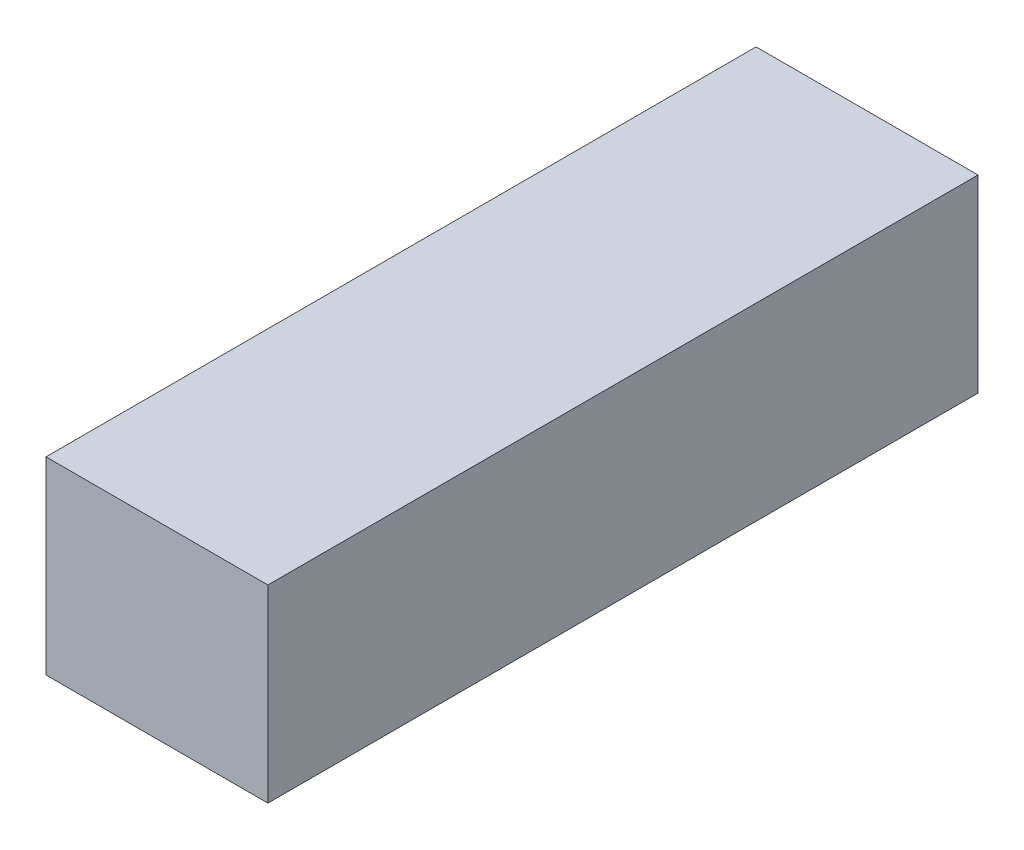
SolidWorks part; units mm, degrees
ref_plane "Front Plane" through (0, 0, 0) normal (0, 0, 1) x (1, 0, 0)
ref_plane "Top Plane" through (0, 0, 0) normal (0, 1, 0) x (1, 0, 0)
ref_plane "Right Plane" through (0, 0, 0) normal (1, 0, 0) x (0, 0, -1)
sketch "Sketch1" plane through (0, 0, 0) normal (0, 0, 1) x (1, 0, 0)
  line L1 (-17.5, -14.9) -> (17.5, -14.9)
  line L2 (-17.5, -14.9) -> (-17.5, 14.9)
  line L3 (-17.5, 14.9) -> (17.5, 14.9)
  line L4 (17.5, -14.9) -> (17.5, 14.9)
  line L5 (-17.5, -14.9) -> (17.5, 14.9) construction
  line L6 (-17.5, 14.9) -> (17.5, -14.9) construction
  point P0 (0, 0)
  dimension "D1" = 35
  dimension "D2" = 29.8
extrude "Boss-Extrude1" add sketch "Sketch1" along normal blind 112
sketch "Sketch2" plane through (0, 0, 112) normal (0, 0, 1) x (1, 0, 0)
  circle A0 centre (0, 0) radius 22.9839
